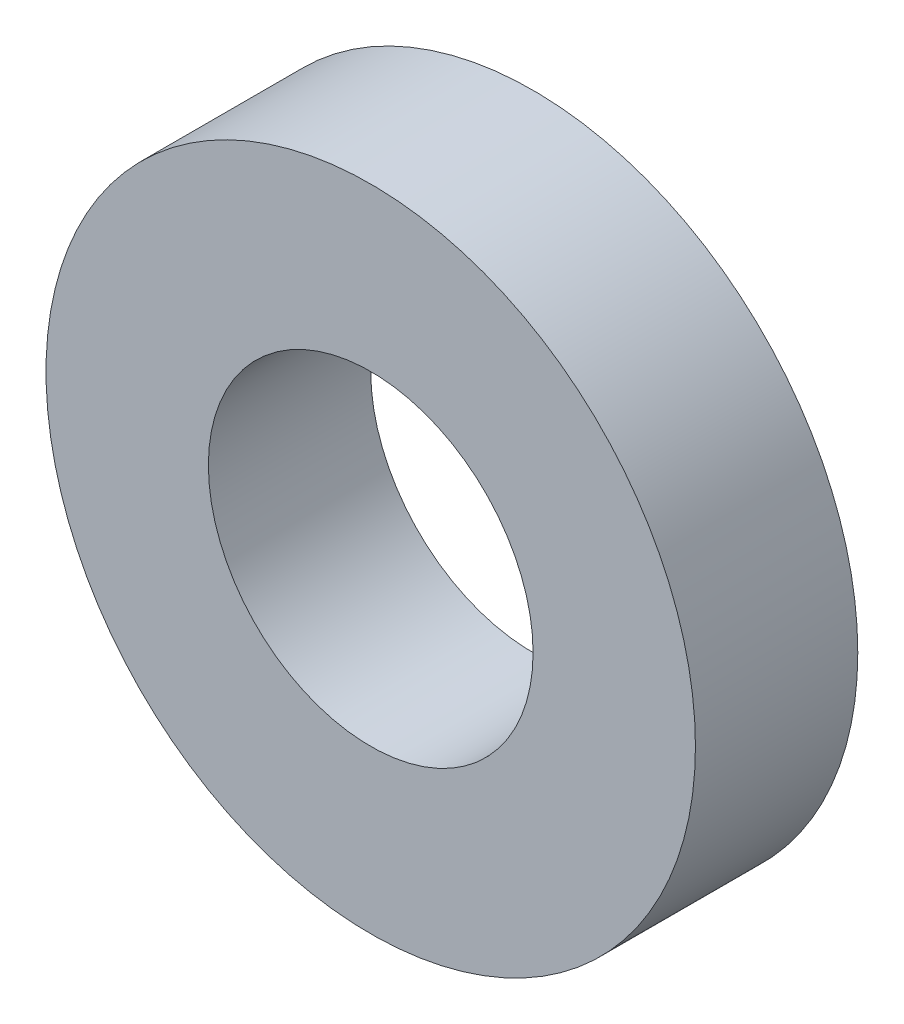
SolidWorks part; units mm, degrees
ref_plane "前视基准面" through (0, 0, 0) normal (0, 0, 1) x (1, 0, 0)
ref_plane "上视基准面" through (0, 0, 0) normal (0, 1, 0) x (1, 0, 0)
ref_plane "右视基准面" through (0, 0, 0) normal (1, 0, 0) x (0, 0, -1)
sketch "草图1" plane through (0, 0, 0) normal (0, 0, 1) x (1, 0, 0)
  circle A0 centre (0, 0) radius 1
  circle A1 centre (0, 0) radius 2
extrude "凸台-拉伸1" add sketch "草图1" along normal blind 1
